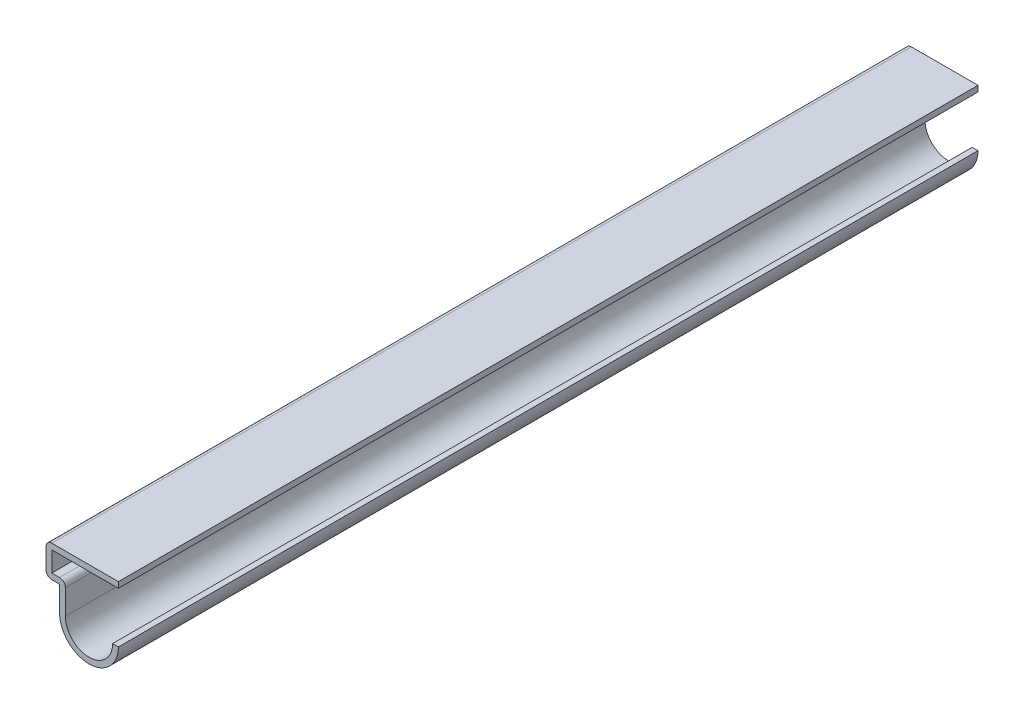
SolidWorks part; units mm, degrees
ref_plane "Front Plane" through (0, 0, 0) normal (0, 0, 1) x (1, 0, 0)
ref_plane "Top Plane" through (0, 0, 0) normal (0, 1, 0) x (1, 0, 0)
ref_plane "Right Plane" through (0, 0, 0) normal (1, 0, 0) x (0, 0, -1)
sketch "Sketch1" plane through (0, 0, 0) normal (0, 0, 1) x (1, 0, 0)
  line L0 (-10.3187, 0) -> (-10.3187, 4.3656)
  line L1 (-10.3187, 4.3656) -> (-12.7, 4.3656)
  line L2 (-12.7, 4.3656) -> (-12.7, 9.9219)
  line L3 (-12.7, 9.9219) -> (0, 9.9219)
  arc A0 (0, 0) -> (-10.3187, 0) centre (-5.1594, 0) cw
  point P2 (0, 0)
  point P9 (0, 0)
  point P10 (0, 0)
  point P11 (0, 0)
  point P12 (0, 0)
  point P13 (1.081, -0.2158)
  point P14 (0, 0)
  dimension "D1" = 12.7
  dimension "D2" = 5.5562
  dimension "D3" = 2.3813
  dimension "D4" = 10.3187
  dimension "D5" = 12.7
  dimension "D6" = 9.525
  dimension "D7" = 15.0813
extrude "Extrude-Thin1" add sketch "Sketch1" against normal blind 150.8125 thin
fillet "Fillet1" radius 1.016 3 edges at (-9.3027, 5.3816, -75.4062) (-12.7, 4.3656, -75.4062) (-12.7, 9.9219, -75.4062)
